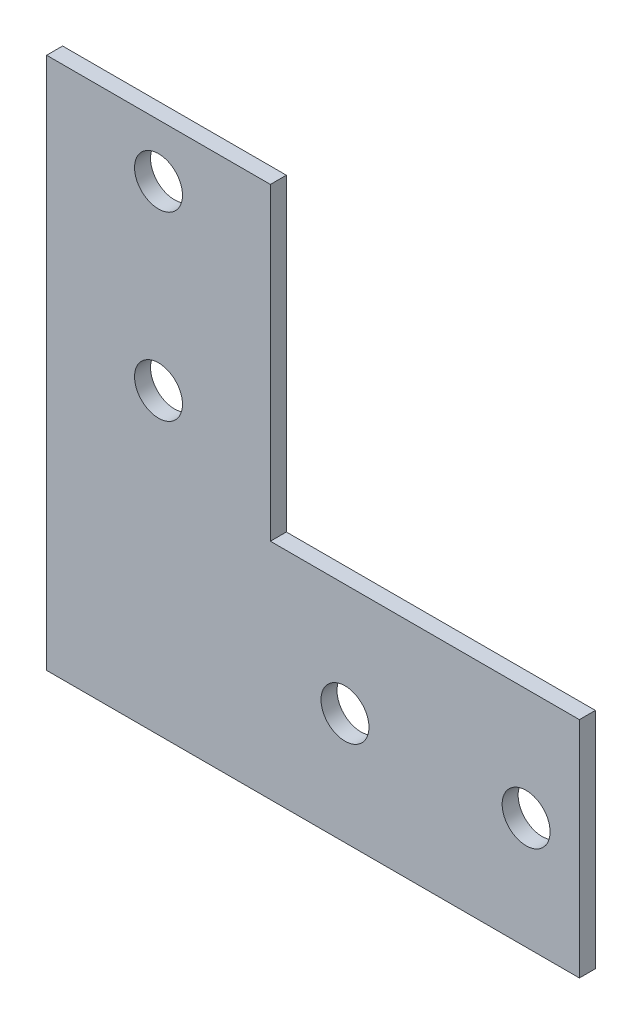
SolidWorks part; units mm, degrees
ref_plane "Спереди" through (0, 0, 0) normal (0, 0, 1) x (1, 0, 0)
ref_plane "Сверху" through (0, 0, 0) normal (0, 1, 0) x (1, 0, 0)
ref_plane "Справа" through (0, 0, 0) normal (1, 0, 0) x (0, 0, -1)
sketch "Эскиз1" plane through (0, 0, 0) normal (0, 0, 1) x (1, 0, 0)
  line L5 (0, 100) -> (0, 0)
  line L6 (0, 0) -> (100, 0)
  line L11 (100, 0) -> (100, 42)
  line L12 (100, 42) -> (42, 42)
  line L16 (42, 42) -> (42, 100)
  line L17 (42, 100) -> (0, 100)
  line L18 (100, 21) -> (90, 21) construction
  line L19 (90, 21) -> (56, 21) construction
  line L20 (21, 100) -> (21, 90) construction
  line L21 (21, 90) -> (21, 56) construction
  circle A6 centre (21, 90) radius 4.5
  circle A7 centre (21, 56) radius 4.5
  circle A8 centre (56, 21) radius 4.5
  circle A9 centre (90, 21) radius 4.5
  dimension "D4" = 10
  dimension "D5" = 34
  dimension "D3" = 9
  dimension "D1" = 100
  dimension "D2" = 42
extrude "Бобышка-Вытянуть1" add sketch "Эскиз1" along normal blind 3
